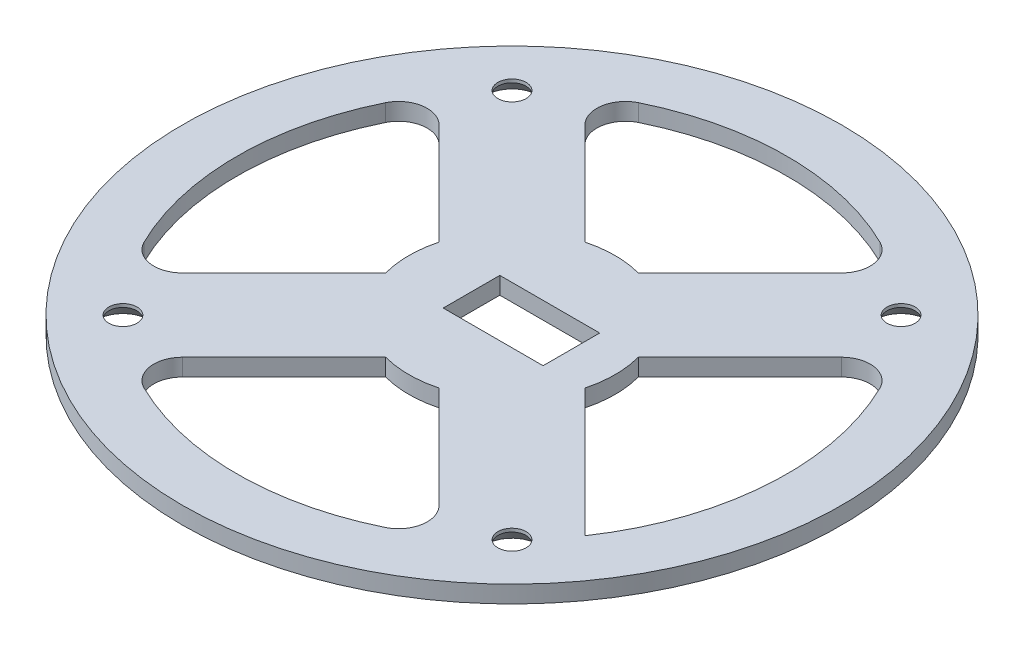
SolidWorks part; units mm, degrees
material "ABS"
ref_plane "Front Plane" through (0, 0, 0) normal (0, 0, 1) x (1, 0, 0)
ref_plane "Top Plane" through (0, 0, 0) normal (0, 1, 0) x (1, 0, 0)
ref_plane "Right Plane" through (0, 0, 0) normal (1, 0, 0) x (0, 0, -1)
sketch "Sketch1" plane through (0, 0, 0) normal (0, 1, 0) x (1, 0, 0)
  line L0 (0, 57.5) -> (0, 0) construction
  line L1 (0, 0) -> (-57.5, 0) construction
  line L2 (-57.5, 0) -> (-40.6586, 40.6586) construction
  line L3 (-40.6586, 40.6586) -> (0, 57.5) construction
  line L4 (-40.6586, 40.6586) -> (0, 0) construction
  line L5 (-3, 4.9375) -> (6.3, 4.9375)
  line L7 (-3, 4.9375) -> (-3, -4.9375)
  line L8 (-3, -4.9375) -> (6.3, -4.9375)
  line L9 (6.3, 4.9375) -> (6.3, -4.9375)
  line L14 (-3, -4.9375) -> (6.3, -4.9375) construction
  circle A0 centre (0, 0) radius 57.5
  circle A1 centre (-33.9411, 33.9411) radius 0.5
  circle A2 centre (33.9411, 33.9411) radius 0.5
  circle A3 centre (33.9411, -33.9411) radius 0.5
  circle A4 centre (-33.9411, -33.9411) radius 0.5
  point P17 (0, 0)
  dimension "D2" = 115
  dimension "D3" = 1
  dimension "D1" = 48
  dimension "D5" = 9.875
  dimension "D7" = 9.3
  dimension "D6" = 3
  dimension "D4" = 4
extrude "Boss-Extrude1" add sketch "Sketch1" along normal blind 3
hole_wizard "CSK for #8 Flat Head Socket Cap Screw1" positions "Sketch3" profile "Sketch2" countersink size "#8" standard "ANSI Inch" end condition through all
sketch "Sketch3" plane through (0, 0, 0) normal (0, -1, 0) x (-1, 0, 0)
  point P0 (33.9411, -33.9411)
  point P3 (-33.9411, -33.9411)
  point P6 (-33.9411, 33.9411)
  point P9 (33.9411, 33.9411)
sketch "Sketch2" plane through (-33.9411, 0, 33.9411) normal (1, 0, 0) x (0, 0, -1)
  line L0 (0, 0) -> (0, 3)
  line L1 (0, 3) -> (2.4574, 3)
  line L2 (2.4574, 3) -> (2.4574, 2.4179)
  line L3 (2.4574, 2.4179) -> (4.5593, 0)
  line L5 (4.5593, 0) -> (0, 0)
  line L6 (-2.4575, 2.4179) -> (-4.5593, 0) construction
  line L11 (0, -6.35) -> (0, 107.95) construction
  dimension "Thru Hole Dia." = 4.9149
  dimension "Thru Hole Depth" = 3
  dimension "Near C'Sink Dia." = 9.1186
  dimension "Near C'Sink Angle" = 82
sketch "Sketch4" plane through (0, 3, 0) normal (0, 1, 0) x (1, 0, 0)
  line L0 (0, 57.5) -> (0, 48) construction
  line L1 (0, 48) -> (0, 38.5) construction
  line L3 (0, 0) -> (-33.9411, 33.9411) construction
  line L4 (-26.9752, 39.7031) -> (-4.6587, 17.3867)
  line L5 (26.9752, 39.7031) -> (4.6587, 17.3867)
  line L6 (39.7031, 26.9752) -> (17.3867, 4.6587)
  line L7 (39.7031, -26.9752) -> (17.3867, -4.6587)
  line L8 (26.9752, -39.7031) -> (4.6587, -17.3867)
  line L9 (-26.9752, -39.7031) -> (-4.6587, -17.3867)
  line L10 (-39.7031, -26.9752) -> (-17.3867, -4.6587)
  line L11 (-39.7031, 26.9752) -> (-17.3867, 4.6587)
  circle A0 centre (0, 0) radius 48 construction
  circle A1 centre (0, 0) radius 38.5 construction
  circle A2 centre (0, 0) radius 57.5 construction
  arc A3 (4.6587, 17.3867) -> (-4.6587, 17.3867) centre (0, 0) ccw
  arc A4 (-26.9752, 39.7031) -> (26.9752, 39.7031) centre (0, 0) cw
  circle A5 centre (0, 0) radius 18 construction
  arc A6 (39.7031, 26.9752) -> (39.7031, -26.9752) centre (0, 0) cw
  arc A7 (17.3867, -4.6587) -> (17.3867, 4.6587) centre (0, 0) ccw
  arc A8 (26.9752, -39.7031) -> (-26.9752, -39.7031) centre (0, 0) cw
  arc A9 (-4.6587, -17.3867) -> (4.6587, -17.3867) centre (0, 0) ccw
  arc A10 (-39.7031, -26.9752) -> (-39.7031, 26.9752) centre (0, 0) cw
  arc A11 (-17.3867, 4.6587) -> (-17.3867, -4.6587) centre (0, 0) ccw
  point P33 (0, 0)
  dimension "D1" = 36
  dimension "D2" = 9
  dimension "D3" = 4
extrude "Cut-Extrude1" cut sketch "Sketch4" against normal through all
fillet "Fillet1" radius 5 7 edges at (-39.7031, 1.5, 26.9752) (-26.9752, 1.5, 39.7031) (26.9752, 1.5, 39.7031) (39.7031, 1.5, -26.9752) (26.9752, 1.5, -39.7031) (-26.9752, 1.5, -39.7031) (-39.7031, 1.5, -26.9752)
sketch "Sketch5" plane through (0, 0, 0) normal (0, -1, 0) x (1, 0, 0)
  line L0 (1.65, -4.9375) -> (1.65, 4.9375) construction
  line L1 (6.3, -4.9375) -> (10.3625, -4.9375)
  line L2 (6.3, -4.9375) -> (6.3, 4.9375)
  line L3 (6.3, 4.9375) -> (10.3625, 4.9375)
  line L4 (10.3625, -4.9375) -> (10.3625, 4.9375)
  line L5 (6.3, -4.9375) -> (-3, -4.9375) construction
  line L6 (-3, 4.9375) -> (6.3, 4.9375) construction
  line L7 (-7.0625, -4.9375) -> (-7.0625, 4.9375)
  line L8 (-3, 4.9375) -> (-7.0625, 4.9375)
  line L9 (-3, -4.9375) -> (-3, 4.9375)
  line L10 (-3, -4.9375) -> (-7.0625, -4.9375)
  dimension "D1" = 4.0625
extrude "Cut-Extrude2" cut sketch "Sketch5" against normal through all
equation "\"D6@Sketch1\"=\"width keep@values@params_print.sldprt\""
equation "\"D7@Sketch1\"=\"pin diameter@values@params_print.sldprt\"+2*\"width keep@values@params_print.sldprt\"+\"print fit@values@params_print.sldprt\""
equation "\"D5@Sketch1\"=9.75 +\"print fit@values@params_print.sldprt\""
equation "\"D1@Boss-Extrude1\"=\"width keep@values@params_print.sldprt\""
equation "\"D2@Sketch4\" = 3 * \"width keep@values@params_print.sldprt\""
equation "\"D1@Sketch5\"=\"width tab@values@params_print.sldprt\"+\"print fit@values@params_print.sldprt\"/2"
